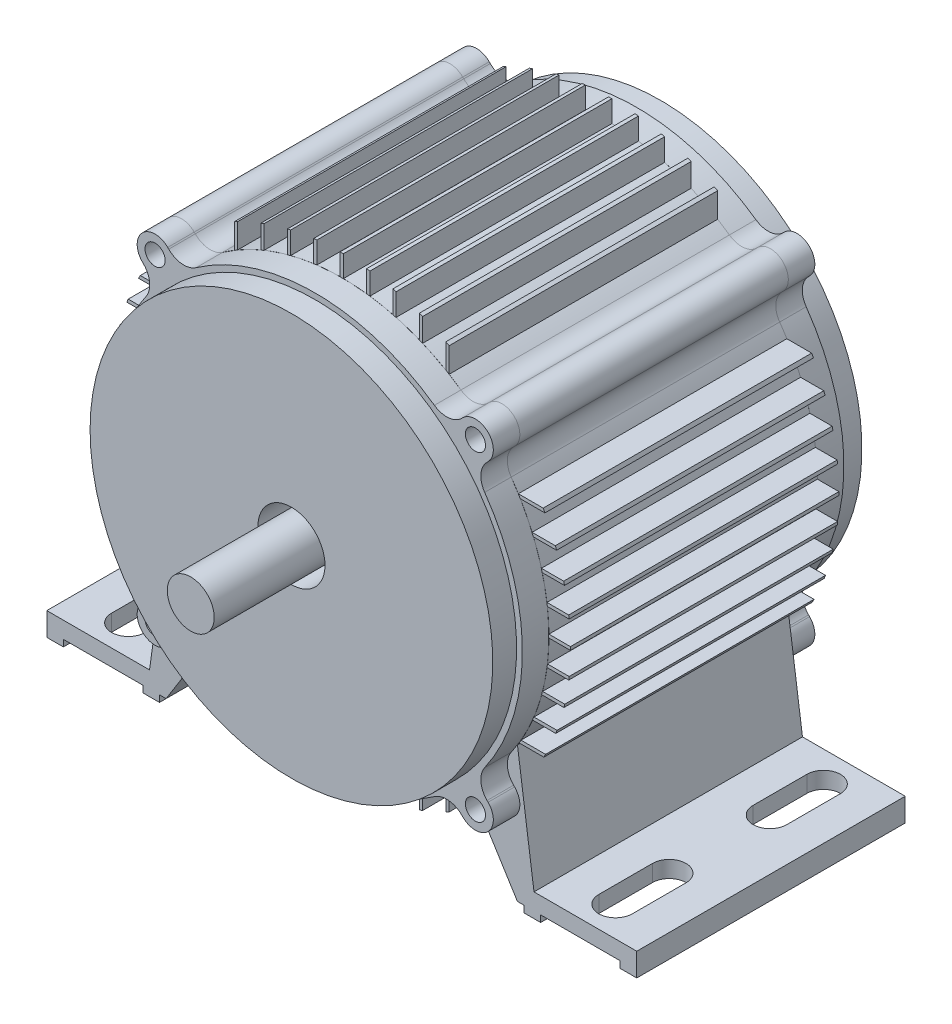
SolidWorks part; units mm, degrees
ref_plane "Front Plane" through (0, 0, 0) normal (0, 0, 1) x (1, 0, 0)
ref_plane "Top Plane" through (0, 0, 0) normal (0, 1, 0) x (1, 0, 0)
ref_plane "Right Plane" through (0, 0, 0) normal (1, 0, 0) x (0, 0, -1)
sketch "Sketch1" plane through (0, 0, 0) normal (0, 0, 1) x (1, 0, 0)
  line L0 (87.9012, -68.1481) -> (57.284, -68.1481)
  line L1 (57.284, -68.1481) -> (52.3831, -32.8719)
  line L2 (52.3831, -32.8719) -> (52.4975, -32.5422)
  line L3 (52.4975, -32.5422) -> (52.705, -32.1337)
  line L4 (52.705, -32.1337) -> (52.7419, -32.0731)
  line L5 (52.7419, -32.0731) -> (52.8389, -31.9131)
  line L6 (52.8389, -31.9131) -> (60.214, -31.9131)
  line L7 (60.214, -31.9131) -> (60.2859, -31.7771)
  line L8 (60.2859, -31.7771) -> (60.2859, -30.9254)
  line L9 (60.2859, -30.9254) -> (53.423, -30.9254)
  line L10 (53.423, -30.9254) -> (56.618, -24.5926)
  line L11 (56.618, -24.5926) -> (56.8668, -24.0119)
  line L12 (56.8668, -24.0119) -> (63.713, -24.0119)
  line L13 (63.713, -24.0119) -> (63.713, -23.0242)
  line L14 (63.713, -23.0242) -> (57.2738, -23.0242)
  line L15 (57.2738, -23.0242) -> (59.4393, -16.6541)
  line L16 (59.4393, -16.6541) -> (59.589, -16.1106)
  line L17 (59.589, -16.1106) -> (66.0327, -16.1106)
  line L18 (66.0327, -16.1106) -> (66.0327, -15.123)
  line L19 (66.0327, -15.123) -> (59.8472, -15.123)
  line L20 (59.8472, -15.123) -> (61.1535, -8.4053)
  line L21 (61.1535, -8.4053) -> (61.1669, -8.3066)
  line L22 (61.1669, -8.3066) -> (67.3482, -8.3066)
  line L23 (67.3482, -8.3066) -> (67.3482, -7.3189)
  line L24 (67.3482, -7.3189) -> (61.293, -7.3189)
  line L25 (61.293, -7.3189) -> (61.7271, -0.4053)
  line L26 (61.7271, -0.4053) -> (67.752, -0.4053)
  line L27 (67.752, -0.4053) -> (67.752, 0.5823)
  line L28 (67.752, 0.5823) -> (61.7257, 0.5823)
  line L29 (61.7257, 0.5823) -> (61.2716, 7.4959)
  line L30 (61.2716, 7.4959) -> (67.3482, 7.4959)
  line L31 (67.3482, 7.4959) -> (67.3482, 8.4836)
  line L32 (67.3482, 8.4836) -> (61.1427, 8.4836)
  line L33 (61.1427, 8.4836) -> (59.7569, 15.4762)
  line L34 (59.7569, 15.4762) -> (65.992, 15.4762)
  line L35 (65.992, 15.4762) -> (65.992, 16.4639)
  line L36 (65.992, 16.4639) -> (59.4923, 16.4639)
  line L37 (59.4923, 16.4639) -> (59.4393, 16.6541)
  line L38 (59.4393, 16.6541) -> (57.1305, 23.3775)
  line L39 (57.1305, 23.3775) -> (63.6491, 23.3775)
  line L40 (63.6491, 23.3775) -> (63.6491, 24.3509)
  line L41 (63.6491, 24.3509) -> (63.6436, 24.3651)
  line L42 (63.6436, 24.3651) -> (56.7163, 24.3651)
  line L43 (56.7163, 24.3651) -> (56.618, 24.5927)
  line L44 (56.618, 24.5927) -> (53.2169, 31.2787)
  line L45 (53.2169, 31.2787) -> (60.2458, 31.2787)
  line L46 (60.2458, 31.2787) -> (60.2459, 31.853)
  line L47 (60.2459, 31.853) -> (60.0255, 32.2664)
  line L48 (60.0255, 32.2664) -> (52.6239, 32.2664)
  line L49 (52.6239, 32.2664) -> (50.07, 36.1025)
  line L50 (50.07, 36.1025) -> (49.9817, 36.356)
  line L51 (49.9817, 36.356) -> (49.6732, 38.3039)
  line L52 (49.6732, 38.3039) -> (49.9817, 40.2519)
  line L53 (49.9817, 40.2519) -> (50.8771, 42.0093)
  line L54 (50.8771, 42.0093) -> (51.5195, 42.7614)
  line L55 (51.5195, 42.7614) -> (52.1506, 43.5004)
  line L56 (52.1506, 43.5004) -> (53.0302, 45.2268)
  line L57 (53.0302, 45.2268) -> (53.3334, 47.1404)
  line L58 (53.3334, 47.1404) -> (53.0302, 49.0541)
  line L59 (53.0302, 49.0541) -> (52.1506, 50.7805)
  line L60 (52.1506, 50.7805) -> (50.7805, 52.1506)
  line L61 (50.7805, 52.1506) -> (49.0542, 53.0302)
  line L62 (49.0542, 53.0302) -> (47.1404, 53.3334)
  line L63 (47.1404, 53.3334) -> (45.2268, 53.0303)
  line L64 (45.2268, 53.0303) -> (43.5003, 52.1506)
  line L65 (43.5003, 52.1506) -> (42.7615, 51.5195)
  line L66 (42.7615, 51.5195) -> (42.0093, 50.8771)
  line L67 (42.0093, 50.8771) -> (40.2519, 49.9816)
  line L68 (40.2519, 49.9816) -> (38.3039, 49.6731)
  line L69 (38.3039, 49.6731) -> (36.356, 49.9817)
  line L70 (36.356, 49.9817) -> (36.1025, 50.07)
  line L71 (36.1025, 50.07) -> (35.5976, 50.4303)
  line L72 (35.5976, 50.4303) -> (32.178, 52.6781)
  line L73 (32.178, 52.6781) -> (32.178, 60.0729)
  line L74 (32.178, 60.0729) -> (31.3526, 60.5077)
  line L75 (31.3526, 60.5077) -> (31.1903, 60.5916)
  line L76 (31.1903, 60.5916) -> (31.1903, 53.2688)
  line L77 (31.1903, 53.2688) -> (28.3991, 54.8077)
  line L78 (28.3991, 54.8077) -> (24.2767, 56.7542)
  line L79 (24.2767, 56.7542) -> (24.2767, 63.6774)
  line L80 (24.2767, 63.6774) -> (23.2891, 64.0452)
  line L81 (23.2891, 64.0452) -> (23.2891, 57.1665)
  line L82 (23.2891, 57.1665) -> (20.6716, 58.1642)
  line L83 (20.6716, 58.1642) -> (16.3755, 59.5167)
  line L84 (16.3755, 59.5167) -> (16.3755, 66.1514)
  line L85 (16.3755, 66.1514) -> (15.3879, 66.3882)
  line L86 (15.3879, 66.3882) -> (15.3878, 59.7796)
  line L87 (15.3878, 59.7796) -> (12.559, 60.4373)
  line L88 (12.559, 60.4373) -> (8.3951, 61.1549)
  line L89 (8.3951, 61.1549) -> (8.3951, 67.6291)
  line L90 (8.3951, 67.6291) -> (7.4074, 67.7444)
  line L91 (7.4074, 67.7444) -> (7.4074, 61.2824)
  line L92 (7.4074, 61.2824) -> (4.2125, 61.5845)
  line L93 (4.2125, 61.5845) -> (0.4938, 61.7264)
  line L94 (0.4938, 61.7264) -> (0.4938, 68.1464)
  line L95 (0.4938, 68.1464) -> (-0.4938, 68.1464)
  line L96 (-0.4938, 68.1464) -> (-0.4938, 61.7264)
  line L97 (-0.4938, 61.7264) -> (-4.2124, 61.5845)
  line L98 (-4.2124, 61.5845) -> (-7.4074, 61.2824)
  line L99 (-7.4074, 61.2824) -> (-7.4074, 67.7444)
  line L100 (-7.4074, 67.7444) -> (-8.3951, 67.6291)
  line L101 (-8.3951, 67.6291) -> (-8.3951, 61.1549)
  line L102 (-8.3951, 61.1549) -> (-12.559, 60.4373)
  line L103 (-12.559, 60.4373) -> (-15.2114, 59.8248)
  line L104 (-15.2114, 59.8248) -> (-15.2114, 66.4288)
  line L105 (-15.2114, 66.4288) -> (-16.199, 66.1949)
  line L106 (-16.199, 66.1949) -> (-16.199, 59.565)
  line L107 (-16.199, 59.565) -> (-20.6716, 58.1642)
  line L108 (-20.6716, 58.1642) -> (-23.1126, 57.2381)
  line L109 (-23.1126, 57.2381) -> (-23.1126, 64.1091)
  line L110 (-23.1126, 64.1091) -> (-24.1002, 63.7444)
  line L111 (-24.1002, 63.7444) -> (-24.1003, 56.8294)
  line L112 (-24.1003, 56.8294) -> (-28.399, 54.8078)
  line L113 (-28.399, 54.8078) -> (-31.0138, 53.3717)
  line L114 (-31.0138, 53.3717) -> (-31.0138, 60.6755)
  line L115 (-31.0138, 60.6755) -> (-31.0267, 60.6755)
  line L116 (-31.0267, 60.6755) -> (-31.3526, 60.5077)
  line L117 (-31.3526, 60.5077) -> (-32.0015, 60.167)
  line L118 (-32.0015, 60.167) -> (-32.0015, 52.7854)
  line L119 (-32.0015, 52.7854) -> (-35.5975, 50.4302)
  line L120 (-35.5975, 50.4302) -> (-36.1024, 50.0701)
  line L121 (-36.1024, 50.0701) -> (-36.3559, 49.9817)
  line L122 (-36.3559, 49.9817) -> (-38.3039, 49.6731)
  line L123 (-38.3039, 49.6731) -> (-40.2519, 49.9816)
  line L124 (-40.2519, 49.9816) -> (-42.0092, 50.877)
  line L125 (-42.0092, 50.877) -> (-42.7614, 51.5195)
  line L126 (-42.7614, 51.5195) -> (-43.5003, 52.1506)
  line L127 (-43.5003, 52.1506) -> (-45.2268, 53.0303)
  line L128 (-45.2268, 53.0303) -> (-47.1404, 53.3334)
  line L129 (-47.1404, 53.3334) -> (-49.0541, 53.0303)
  line L130 (-49.0541, 53.0303) -> (-50.7805, 52.1506)
  line L131 (-50.7805, 52.1506) -> (-52.1506, 50.7805)
  line L132 (-52.1506, 50.7805) -> (-53.0302, 49.0541)
  line L133 (-53.0302, 49.0541) -> (-53.3333, 47.1404)
  line L134 (-53.3333, 47.1404) -> (-53.0302, 45.2268)
  line L135 (-53.0302, 45.2268) -> (-52.1506, 43.5004)
  line L136 (-52.1506, 43.5004) -> (-51.5195, 42.7614)
  line L137 (-51.5195, 42.7614) -> (-50.877, 42.0093)
  line L138 (-50.877, 42.0093) -> (-49.9816, 40.2519)
  line L139 (-49.9816, 40.2519) -> (-49.6731, 38.3039)
  line L140 (-49.6731, 38.3039) -> (-49.9816, 36.3559)
  line L141 (-49.9816, 36.3559) -> (-50.07, 36.1025)
  line L142 (-50.07, 36.1025) -> (-52.6239, 32.2664)
  line L143 (-52.6239, 32.2664) -> (-60.0254, 32.2664)
  line L144 (-60.0254, 32.2664) -> (-60.5459, 31.2787)
  line L145 (-60.5459, 31.2787) -> (-53.2169, 31.2787)
  line L146 (-53.2169, 31.2787) -> (-56.6179, 24.5927)
  line L147 (-56.6179, 24.5927) -> (-56.7162, 24.3651)
  line L148 (-56.7162, 24.3651) -> (-63.6436, 24.3651)
  line L149 (-63.6436, 24.3651) -> (-64.0129, 23.3775)
  line L150 (-64.0129, 23.3775) -> (-57.1304, 23.3775)
  line L151 (-57.1304, 23.3775) -> (-59.4393, 16.6541)
  line L152 (-59.4393, 16.6541) -> (-59.4923, 16.4639)
  line L153 (-59.4923, 16.4639) -> (-66.1295, 16.4639)
  line L154 (-66.1295, 16.4639) -> (-66.3676, 15.4762)
  line L155 (-66.3676, 15.4762) -> (-59.7569, 15.4762)
  line L156 (-59.7569, 15.4762) -> (-61.1426, 8.4836)
  line L157 (-61.1426, 8.4836) -> (-67.6181, 8.4836)
  line L158 (-67.6181, 8.4836) -> (-67.7346, 7.4959)
  line L159 (-67.7346, 7.4959) -> (-61.2716, 7.4959)
  line L160 (-61.2716, 7.4959) -> (-61.7256, 0.5823)
  line L161 (-61.7256, 0.5823) -> (-68.1457, 0.5823)
  line L162 (-68.1457, 0.5823) -> (-68.1481, 0)
  line L163 (-68.1481, 0) -> (-68.147, -0.4053)
  line L164 (-68.147, -0.4053) -> (-61.727, -0.4053)
  line L165 (-61.727, -0.4053) -> (-61.293, -7.3189)
  line L166 (-61.293, -7.3189) -> (-67.754, -7.3189)
  line L167 (-67.754, -7.3189) -> (-67.64, -8.3066)
  line L168 (-67.64, -8.3066) -> (-61.1669, -8.3066)
  line L169 (-61.1669, -8.3066) -> (-61.1534, -8.4053)
  line L170 (-61.1534, -8.4053) -> (-59.8472, -15.123)
  line L171 (-59.8472, -15.123) -> (-66.449, -15.123)
  line L172 (-66.449, -15.123) -> (-66.2164, -16.1106)
  line L173 (-66.2164, -16.1106) -> (-59.5889, -16.1106)
  line L174 (-59.5889, -16.1106) -> (-59.4393, -16.6541)
  line L175 (-59.4393, -16.6541) -> (-57.2737, -23.0242)
  line L176 (-57.2737, -23.0242) -> (-64.1409, -23.0242)
  line L177 (-64.1409, -23.0242) -> (-63.7778, -24.0118)
  line L178 (-63.7778, -24.0118) -> (-56.8667, -24.0119)
  line L179 (-56.8667, -24.0119) -> (-56.618, -24.5926)
  line L180 (-56.618, -24.5926) -> (-53.4229, -30.9254)
  line L181 (-53.4229, -30.9254) -> (-60.7271, -30.9254)
  line L182 (-60.7271, -30.9254) -> (-60.2139, -31.9131)
  line L183 (-60.2139, -31.9131) -> (-52.8389, -31.9131)
  line L184 (-52.8389, -31.9131) -> (-52.7419, -32.0731)
  line L185 (-52.7419, -32.0731) -> (-52.6941, -32.1515)
  line L186 (-52.6941, -32.1515) -> (-52.486, -32.5609)
  line L187 (-52.486, -32.5609) -> (-52.3812, -32.8579)
  line L188 (-52.3812, -32.8579) -> (-57.284, -68.1481)
  line L189 (-57.284, -68.1481) -> (-87.9012, -68.1481)
  line L190 (-87.9012, -68.1481) -> (-87.9012, -75.0617)
  line L191 (-87.9012, -75.0617) -> (-82.963, -75.0617)
  line L192 (-82.963, -75.0617) -> (-82.963, -73.0864)
  line L193 (-82.963, -73.0864) -> (-59.2593, -73.0864)
  line L194 (-59.2593, -73.0864) -> (-59.2593, -75.0617)
  line L195 (-59.2593, -75.0617) -> (-54.321, -75.0617)
  line L196 (-54.321, -75.0617) -> (-54.321, -73.0864)
  line L197 (-54.321, -73.0864) -> (-52.3457, -73.0864)
  line L198 (-52.3457, -73.0864) -> (-37.7288, -49.6994)
  line L199 (-37.7288, -49.6994) -> (-36.3558, -49.9816)
  line L200 (-36.3558, -49.9816) -> (-36.1024, -50.07)
  line L201 (-36.1024, -50.07) -> (-35.5975, -50.4302)
  line L202 (-35.5975, -50.4302) -> (-32.0015, -52.7854)
  line L203 (-32.0015, -52.7854) -> (-32.0015, -60.167)
  line L204 (-32.0015, -60.167) -> (-31.3526, -60.5077)
  line L205 (-31.3526, -60.5077) -> (-31.0138, -60.682)
  line L206 (-31.0138, -60.682) -> (-31.0138, -53.3717)
  line L207 (-31.0138, -53.3717) -> (-28.399, -54.8077)
  line L208 (-28.399, -54.8077) -> (-24.1002, -56.8293)
  line L209 (-24.1002, -56.8293) -> (-24.1002, -63.7444)
  line L210 (-24.1002, -63.7444) -> (-23.1126, -64.1091)
  line L211 (-23.1126, -64.1091) -> (-23.1126, -57.2381)
  line L212 (-23.1126, -57.2381) -> (-20.6716, -58.1642)
  line L213 (-20.6716, -58.1642) -> (-16.199, -59.565)
  line L214 (-16.199, -59.565) -> (-16.199, -66.1949)
  line L215 (-16.199, -66.1949) -> (-15.2114, -66.4288)
  line L216 (-15.2114, -66.4288) -> (-15.2114, -59.8248)
  line L217 (-15.2114, -59.8248) -> (-12.559, -60.4373)
  line L218 (-12.559, -60.4373) -> (-8.3951, -61.1548)
  line L219 (-8.3951, -61.1548) -> (-8.3951, -67.6291)
  line L220 (-8.3951, -67.6291) -> (-7.4074, -67.7444)
  line L221 (-7.4074, -67.7444) -> (-7.4074, -61.2823)
  line L222 (-7.4074, -61.2823) -> (-4.2124, -61.5845)
  line L223 (-4.2124, -61.5845) -> (-0.4938, -61.7264)
  line L224 (-0.4938, -61.7264) -> (-0.4938, -68.1464)
  line L225 (-0.4938, -68.1464) -> (0.4938, -68.1464)
  line L226 (0.4938, -68.1464) -> (0.4938, -61.7264)
  line L227 (0.4938, -61.7264) -> (4.2125, -61.5845)
  line L228 (4.2125, -61.5845) -> (7.4074, -61.2823)
  line L229 (7.4074, -61.2823) -> (7.4074, -67.7444)
  line L230 (7.4074, -67.7444) -> (8.3951, -67.6291)
  line L231 (8.3951, -67.6291) -> (8.3951, -61.1548)
  line L232 (8.3951, -61.1548) -> (12.559, -60.4372)
  line L233 (12.559, -60.4372) -> (15.3879, -59.7796)
  line L234 (15.3879, -59.7796) -> (15.3879, -66.3882)
  line L235 (15.3879, -66.3882) -> (16.3755, -66.1514)
  line L236 (16.3755, -66.1514) -> (16.3755, -59.5167)
  line L237 (16.3755, -59.5167) -> (20.6716, -58.1643)
  line L238 (20.6716, -58.1643) -> (23.2891, -57.1665)
  line L239 (23.2891, -57.1665) -> (23.2891, -64.0452)
  line L240 (23.2891, -64.0452) -> (24.2767, -63.6774)
  line L241 (24.2767, -63.6774) -> (24.2767, -56.7542)
  line L242 (24.2767, -56.7542) -> (28.3991, -54.8077)
  line L243 (28.3991, -54.8077) -> (31.1903, -53.2687)
  line L244 (31.1903, -53.2687) -> (31.1903, -60.5915)
  line L245 (31.1903, -60.5915) -> (31.3526, -60.5077)
  line L246 (31.3526, -60.5077) -> (32.178, -60.0729)
  line L247 (32.178, -60.0729) -> (32.178, -52.678)
  line L248 (32.178, -52.678) -> (35.5976, -50.4303)
  line L249 (35.5976, -50.4303) -> (36.2231, -49.9828)
  line L250 (36.2231, -49.9828) -> (36.2811, -49.9636)
  line L251 (36.2811, -49.9636) -> (37.7132, -49.6743)
  line L252 (37.7132, -49.6743) -> (52.3457, -73.0864)
  line L253 (52.3457, -73.0864) -> (54.321, -73.0864)
  line L254 (54.321, -73.0864) -> (54.321, -75.0617)
  line L255 (54.321, -75.0617) -> (59.2593, -75.0617)
  line L256 (59.2593, -75.0617) -> (59.2593, -73.0864)
  line L257 (59.2593, -73.0864) -> (82.963, -73.0864)
  line L258 (82.963, -73.0864) -> (82.963, -75.0617)
  line L259 (82.963, -75.0617) -> (87.9012, -75.0617)
  line L260 (87.9012, -75.0617) -> (87.9012, -68.1481)
  line L261 (0, -68.1464) -> (0, 68.1464) construction
sketch "Sketch2" plane through (0, 0, 0) normal (0, 0, 1) x (1, 0, 0)
  line L0 (0, 0) -> (0, 81.9085) construction
  line L1 (-45.607, 45.607) -> (-81.6783, 81.6783) construction
  line L2 (0, 0) -> (-32.0015, 32.0015) construction
  line L3 (0, 0) -> (-81.6783, 81.6783) construction
  line L4 (-32.0015, 60.167) -> (-32.0015, 52.7854) construction
  line L5 (-51.1961, 43.6527) -> (-51.5014, 43.958)
  line L6 (-43.6527, 51.1961) -> (-43.958, 51.5014)
  line L7 (-31.0138, 53.3717) -> (-31.0138, 60.6755) construction
  line L8 (-3.7717, -3.7717) -> (-85.45, 77.9066) construction
  line L9 (0, 0) -> (0, -101.5619) construction
  line L10 (-24.1002, 63.7444) -> (-24.1003, 56.8294) construction
  line L11 (-23.1126, 57.2381) -> (-23.1126, 64.1091) construction
  line L12 (-16.199, 66.1949) -> (-16.199, 59.565) construction
  line L13 (-15.2114, 59.8248) -> (-15.2114, 66.4288) construction
  line L14 (-8.3951, 67.6291) -> (-8.3951, 61.1549) construction
  line L15 (-7.4074, 61.2824) -> (-7.4074, 67.7444) construction
  line L16 (-0.4938, 68.1464) -> (-0.4938, 61.7264) construction
  line L17 (-52.6239, 32.2664) -> (-60.0254, 32.2664) construction
  line L18 (-60.5459, 31.2787) -> (-53.2169, 31.2787) construction
  line L19 (-56.7162, 24.3651) -> (-63.6436, 24.3651) construction
  line L20 (-64.0129, 23.3775) -> (-57.1304, 23.3775) construction
  line L21 (-59.4923, 16.4639) -> (-66.1295, 16.4639) construction
  line L22 (-66.3676, 15.4762) -> (-59.7569, 15.4762) construction
  line L23 (-61.1426, 8.4836) -> (-67.6181, 8.4836) construction
  line L24 (-67.7346, 7.4959) -> (-61.2716, 7.4959) construction
  line L25 (-61.7256, 0.5823) -> (-68.1457, 0.5823) construction
  line L26 (-68.147, -0.4053) -> (-61.727, -0.4053) construction
  line L27 (-61.293, -7.3189) -> (-67.754, -7.3189) construction
  line L28 (-67.64, -8.3066) -> (-61.1669, -8.3066) construction
  line L29 (-59.8472, -15.123) -> (-66.449, -15.123) construction
  line L30 (-66.2164, -16.1106) -> (-59.5889, -16.1106) construction
  line L31 (-57.2737, -23.0242) -> (-64.1409, -23.0242) construction
  line L32 (-63.7778, -24.0118) -> (-56.8667, -24.0119) construction
  line L33 (-53.4229, -30.9254) -> (-60.7271, -30.9254) construction
  line L34 (-60.2139, -31.9131) -> (-52.8389, -31.9131) construction
  line L35 (-52.3812, -32.8579) -> (-57.284, -68.1481) construction
  line L36 (-52.3457, -73.0864) -> (-37.7288, -49.6994) construction
  line L37 (-54.321, -73.0864) -> (-52.3457, -73.0864) construction
  line L38 (-54.321, -75.0617) -> (-54.321, -73.0864) construction
  line L39 (-59.2593, -75.0617) -> (-54.321, -75.0617) construction
  line L40 (-59.2593, -73.0864) -> (-59.2593, -75.0617) construction
  line L41 (-82.963, -73.0864) -> (-59.2593, -73.0864) construction
  line L42 (-57.284, -68.1481) -> (-87.9012, -68.1481) construction
  line L43 (-87.9012, -68.1481) -> (-87.9012, -75.0617) construction
  line L44 (-87.9012, -75.0617) -> (-82.963, -75.0617) construction
  line L45 (-82.963, -75.0617) -> (-82.963, -73.0864) construction
  line L46 (-32.0015, -52.7854) -> (-32.0015, -60.167) construction
  line L47 (-31.0138, -60.682) -> (-31.0138, -53.3717) construction
  line L48 (-24.1002, -56.8293) -> (-24.1002, -63.7444) construction
  line L49 (-23.1126, -64.1091) -> (-23.1126, -57.2381) construction
  line L50 (-16.199, -59.565) -> (-16.199, -66.1949) construction
  line L51 (-15.2114, -66.4288) -> (-15.2114, -59.8248) construction
  line L52 (-8.3951, -61.1548) -> (-8.3951, -67.6291) construction
  line L53 (-7.4074, -67.7444) -> (-7.4074, -61.2823) construction
  line L54 (-0.4938, -61.7264) -> (-0.4938, -68.1464) construction
  line L55 (-32.0015, 60.167) -> (-32.0015, 52.7854)
  line L56 (-31.0138, 53.3717) -> (-31.0138, 60.6801)
  line L57 (-24.1002, 63.7444) -> (-24.1003, 56.8293)
  line L58 (-23.1126, 57.2381) -> (-23.1126, 64.1091)
  line L59 (-16.199, 66.1949) -> (-16.199, 59.565)
  line L60 (-15.2114, 59.8248) -> (-15.2114, 66.4288)
  line L61 (-8.3951, 67.6291) -> (-8.3951, 61.1549)
  line L62 (-7.4074, 61.2823) -> (-7.4074, 67.7444)
  line L63 (-0.4938, 68.1464) -> (-0.4938, 61.7264)
  line L64 (-52.6239, 32.2664) -> (-60.0254, 32.2664)
  line L65 (-60.5459, 31.2787) -> (-53.2169, 31.2787)
  line L66 (-56.7163, 24.3651) -> (-63.6436, 24.3651)
  line L67 (-64.0129, 23.3775) -> (-57.1305, 23.3775)
  line L68 (-59.4923, 16.4639) -> (-66.1295, 16.4639)
  line L69 (-66.3676, 15.4762) -> (-59.7569, 15.4762)
  line L70 (-61.1427, 8.4836) -> (-67.6181, 8.4836)
  line L71 (-67.7346, 7.4959) -> (-61.2716, 7.4959)
  line L72 (-61.7256, 0.5823) -> (-68.1457, 0.5823)
  line L73 (-68.147, -0.4053) -> (-61.7271, -0.4053)
  line L74 (-61.293, -7.3189) -> (-67.754, -7.3189)
  line L75 (-67.64, -8.3066) -> (-61.167, -8.3066)
  line L76 (-59.8472, -15.123) -> (-66.449, -15.123)
  line L77 (-66.2164, -16.1106) -> (-59.5889, -16.1106)
  line L78 (-57.2737, -23.0242) -> (-64.1409, -23.0242)
  line L79 (-63.7778, -24.0118) -> (-56.8667, -24.0119)
  line L80 (-53.423, -30.9254) -> (-60.7271, -30.9254)
  line L81 (-60.2139, -31.9131) -> (-52.8389, -31.9131)
  line L82 (-52.3586, -32.6952) -> (-57.284, -68.1481)
  line L83 (-52.3457, -73.0864) -> (-37.3725, -49.1293)
  line L84 (-54.321, -73.0864) -> (-52.3457, -73.0864)
  line L85 (-54.321, -75.0617) -> (-54.321, -73.0864)
  line L86 (-59.2593, -75.0617) -> (-54.321, -75.0617)
  line L87 (-59.2593, -73.0864) -> (-59.2593, -75.0617)
  line L88 (-82.963, -73.0864) -> (-59.2593, -73.0864)
  line L89 (-57.284, -68.1481) -> (-87.9012, -68.1481)
  line L90 (-87.9012, -68.1481) -> (-87.9012, -75.0617)
  line L91 (-87.9012, -75.0617) -> (-82.963, -75.0617)
  line L92 (-82.963, -75.0617) -> (-82.963, -73.0864)
  line L93 (-32.0015, -52.7854) -> (-32.0015, -60.167)
  line L94 (-31.0138, -60.682) -> (-31.0138, -53.3717)
  line L95 (-24.1002, -56.8293) -> (-24.1002, -63.7444)
  line L96 (-23.1126, -64.1091) -> (-23.1126, -57.2381)
  line L97 (-16.199, -59.565) -> (-16.199, -66.1949)
  line L98 (-15.2114, -66.4288) -> (-15.2114, -59.8248)
  line L99 (-8.3951, -61.1549) -> (-8.3951, -67.6291)
  line L100 (-7.4074, -67.7444) -> (-7.4074, -61.2823)
  line L101 (-0.4938, -61.7264) -> (-0.4938, -68.1464)
  line L102 (0, 0) -> (32.0015, 32.0015) construction
  line L103 (45.607, 45.607) -> (81.6783, 81.6783) construction
  line L104 (0.4938, -61.7264) -> (0.4938, -68.1464)
  line L105 (7.4074, -67.7444) -> (7.4074, -61.2823)
  line L106 (8.3951, -61.1549) -> (8.3951, -67.6291)
  line L107 (15.2114, -66.4288) -> (15.2114, -59.8248)
  line L108 (16.199, -59.565) -> (16.199, -66.1949)
  line L109 (23.1126, -64.1091) -> (23.1126, -57.2381)
  line L110 (24.1002, -56.8293) -> (24.1002, -63.7444)
  line L111 (31.0138, -60.682) -> (31.0138, -53.3717)
  line L112 (32.0015, -52.7854) -> (32.0015, -60.167)
  line L113 (82.963, -75.0617) -> (82.963, -73.0864)
  line L114 (87.9012, -75.0617) -> (82.963, -75.0617)
  line L115 (87.9012, -68.1481) -> (87.9012, -75.0617)
  line L116 (57.284, -68.1481) -> (87.9012, -68.1481)
  line L117 (82.963, -73.0864) -> (59.2593, -73.0864)
  line L118 (59.2593, -73.0864) -> (59.2593, -75.0617)
  line L119 (59.2593, -75.0617) -> (54.321, -75.0617)
  line L120 (54.321, -75.0617) -> (54.321, -73.0864)
  line L121 (54.321, -73.0864) -> (52.3457, -73.0864)
  line L122 (52.3457, -73.0864) -> (37.3725, -49.1293)
  line L123 (52.3586, -32.6952) -> (57.284, -68.1481)
  line L124 (60.2139, -31.9131) -> (52.8389, -31.9131)
  line L125 (53.423, -30.9254) -> (60.7271, -30.9254)
  line L126 (63.7778, -24.0118) -> (56.8667, -24.0119)
  line L127 (57.2737, -23.0242) -> (64.1409, -23.0242)
  line L128 (66.2164, -16.1106) -> (59.5889, -16.1106)
  line L129 (59.8472, -15.123) -> (66.449, -15.123)
  line L130 (67.64, -8.3066) -> (61.167, -8.3066)
  line L131 (61.293, -7.3189) -> (67.754, -7.3189)
  line L132 (68.147, -0.4053) -> (61.7271, -0.4053)
  line L133 (61.7256, 0.5823) -> (68.1457, 0.5823)
  line L134 (67.7346, 7.4959) -> (61.2716, 7.4959)
  line L135 (61.1427, 8.4836) -> (67.6181, 8.4836)
  line L136 (66.3676, 15.4762) -> (59.7569, 15.4762)
  line L137 (59.4923, 16.4639) -> (66.1295, 16.4639)
  line L138 (64.0129, 23.3775) -> (57.1305, 23.3775)
  line L139 (56.7163, 24.3651) -> (63.6436, 24.3651)
  line L140 (60.5459, 31.2787) -> (53.2169, 31.2787)
  line L141 (52.6239, 32.2664) -> (60.0254, 32.2664)
  line L142 (0.4938, 68.1464) -> (0.4938, 61.7264)
  line L143 (7.4074, 61.2823) -> (7.4074, 67.7444)
  line L144 (8.3951, 67.6291) -> (8.3951, 61.1549)
  line L145 (15.2114, 59.8248) -> (15.2114, 66.4288)
  line L146 (16.199, 66.1949) -> (16.199, 59.565)
  line L147 (23.1126, 57.2381) -> (23.1126, 64.1091)
  line L148 (24.1002, 63.7444) -> (24.1003, 56.8293)
  line L149 (31.0138, 53.3717) -> (31.0138, 60.6801)
  line L150 (32.0015, 60.167) -> (32.0015, 52.7854)
  line L151 (43.6527, 51.1961) -> (43.958, 51.5014)
  line L152 (51.1961, 43.6527) -> (51.5014, 43.958)
  arc A0 (-50.4921, 35.5097) -> (-52.6239, 32.2664) centre (0, 0) ccw
  circle A1 centre (-47.7297, 47.7297) radius 3.0019
  arc A2 (-43.958, 51.5014) -> (-51.5014, 43.958) centre (-47.7297, 47.7297) ccw
  arc A3 (-0.4938, 61.7264) -> (-7.4074, 61.2823) centre (0, 0) ccw
  arc A4 (-43.6527, 51.1961) -> (-35.5097, 50.4921) centre (-39.1626, 55.6863) ccw
  arc A5 (-51.1961, 43.6527) -> (-50.4921, 35.5097) centre (-55.6863, 39.1626) cw
  arc A6 (0.4938, 68.1446) -> (-0.4938, 68.1446) centre (0, 0) ccw
  arc A7 (-32.0015, -60.165) -> (-31.0138, -60.6801) centre (0, 0) ccw
  arc A8 (-24.1002, -63.7425) -> (-23.1126, -64.1072) centre (0, 0) ccw
  arc A9 (-16.199, -66.193) -> (-15.2114, -66.427) centre (0, 0) ccw
  arc A10 (-8.3951, -67.6273) -> (-7.4074, -67.7426) centre (0, 0) ccw
  arc A11 (-60.7252, -30.9254) -> (-60.212, -31.9131) centre (0, 0) ccw
  arc A12 (-64.139, -23.0242) -> (-63.7759, -24.0118) centre (0, 0) ccw
  arc A13 (-66.4471, -15.123) -> (-66.2146, -16.1106) centre (0, 0) ccw
  arc A14 (-67.7522, -7.3189) -> (-67.6382, -8.3066) centre (0, 0) ccw
  arc A15 (-68.1439, 0.5823) -> (-68.1452, -0.4053) centre (0, 0) ccw
  arc A16 (-66.1277, 16.4639) -> (-66.3658, 15.4762) centre (0, 0) ccw
  arc A17 (-63.6417, 24.3651) -> (-64.0111, 23.3775) centre (0, 0) ccw
  arc A18 (-60.0234, 32.2664) -> (-60.544, 31.2787) centre (0, 0) ccw
  arc A19 (-23.1126, 64.1072) -> (-24.1002, 63.7425) centre (0, 0) ccw
  arc A20 (-15.2114, 66.427) -> (-16.199, 66.193) centre (0, 0) ccw
  arc A21 (-7.4074, 67.7426) -> (-8.3951, 67.6273) centre (0, 0) ccw
  arc A22 (-0.4938, -68.1446) -> (0.4938, -68.1446) centre (0, 0) ccw
  arc A23 (-31.0138, 60.6801) -> (-32.0015, 60.165) centre (0, 0) ccw
  arc A24 (-67.6162, 8.4836) -> (-67.7329, 7.4959) centre (0, 0) ccw
  arc A25 (-7.4074, -61.2823) -> (-0.4938, -61.7264) centre (0, 0) ccw
  arc A26 (-15.2114, -59.8248) -> (-8.3951, -61.1549) centre (0, 0) ccw
  arc A27 (-23.1126, -57.2381) -> (-16.199, -59.565) centre (0, 0) ccw
  arc A28 (-31.0138, -53.3717) -> (-24.1002, -56.8293) centre (0, 0) ccw
  arc A29 (-37.3725, -49.1293) -> (-32.0015, -52.7854) centre (0, 0) ccw
  arc A30 (-52.8389, -31.9131) -> (-52.3586, -32.6952) centre (0, 0) ccw
  arc A31 (-56.8667, -24.0119) -> (-53.423, -30.9254) centre (0, 0) ccw
  arc A32 (-59.5889, -16.1106) -> (-57.2737, -23.0242) centre (0, 0) ccw
  arc A33 (-61.167, -8.3066) -> (-59.8472, -15.123) centre (0, 0) ccw
  arc A34 (-61.7271, -0.4053) -> (-61.293, -7.3189) centre (0, 0) ccw
  arc A35 (-61.2716, 7.4959) -> (-61.7256, 0.5823) centre (0, 0) ccw
  arc A36 (-59.7569, 15.4762) -> (-61.1427, 8.4836) centre (0, 0) ccw
  arc A37 (-57.1305, 23.3775) -> (-59.4923, 16.4639) centre (0, 0) ccw
  arc A38 (-53.2169, 31.2787) -> (-56.7163, 24.3651) centre (0, 0) ccw
  arc A39 (-32.0015, 52.7854) -> (-35.5097, 50.4921) centre (0, 0) ccw
  arc A40 (-24.1003, 56.8293) -> (-31.0138, 53.3717) centre (0, 0) ccw
  arc A41 (-16.199, 59.565) -> (-23.1126, 57.2381) centre (0, 0) ccw
  arc A42 (-8.3951, 61.1549) -> (-15.2114, 59.8248) centre (0, 0) ccw
  arc A43 (8.3951, 61.1549) -> (15.2114, 59.8248) centre (0, 0) cw
  arc A44 (16.199, 59.565) -> (23.1126, 57.2381) centre (0, 0) cw
  arc A45 (24.1003, 56.8293) -> (31.0138, 53.3717) centre (0, 0) cw
  arc A46 (32.0015, 52.7854) -> (35.5097, 50.4921) centre (0, 0) cw
  arc A47 (53.2169, 31.2787) -> (56.7163, 24.3651) centre (0, 0) cw
  arc A48 (57.1305, 23.3775) -> (59.4923, 16.4639) centre (0, 0) cw
  arc A49 (59.7569, 15.4762) -> (61.1427, 8.4836) centre (0, 0) cw
  arc A50 (61.2716, 7.4959) -> (61.7256, 0.5823) centre (0, 0) cw
  arc A51 (61.7271, -0.4053) -> (61.293, -7.3189) centre (0, 0) cw
  arc A52 (61.167, -8.3066) -> (59.8472, -15.123) centre (0, 0) cw
  arc A53 (59.5889, -16.1106) -> (57.2737, -23.0242) centre (0, 0) cw
  arc A54 (56.8667, -24.0119) -> (53.423, -30.9254) centre (0, 0) cw
  arc A55 (52.8389, -31.9131) -> (52.3586, -32.6952) centre (0, 0) cw
  arc A56 (37.3725, -49.1293) -> (32.0015, -52.7854) centre (0, 0) cw
  arc A57 (31.0138, -53.3717) -> (24.1002, -56.8293) centre (0, 0) cw
  arc A58 (23.1126, -57.2381) -> (16.199, -59.565) centre (0, 0) cw
  arc A59 (15.2114, -59.8248) -> (8.3951, -61.1549) centre (0, 0) cw
  arc A60 (7.4074, -61.2823) -> (0.4938, -61.7264) centre (0, 0) cw
  arc A61 (67.6162, 8.4836) -> (67.7329, 7.4959) centre (0, 0) cw
  arc A62 (31.0138, 60.6801) -> (32.0015, 60.165) centre (0, 0) cw
  arc A63 (7.4074, 67.7426) -> (8.3951, 67.6273) centre (0, 0) cw
  arc A64 (15.2114, 66.427) -> (16.199, 66.193) centre (0, 0) cw
  arc A65 (23.1126, 64.1072) -> (24.1002, 63.7425) centre (0, 0) cw
  arc A66 (60.0234, 32.2664) -> (60.544, 31.2787) centre (0, 0) cw
  arc A67 (63.6417, 24.3651) -> (64.0111, 23.3775) centre (0, 0) cw
  arc A68 (66.1277, 16.4639) -> (66.3658, 15.4762) centre (0, 0) cw
  arc A69 (68.1439, 0.5823) -> (68.1452, -0.4053) centre (0, 0) cw
  arc A70 (67.7522, -7.3189) -> (67.6382, -8.3066) centre (0, 0) cw
  arc A71 (66.4471, -15.123) -> (66.2146, -16.1106) centre (0, 0) cw
  arc A72 (64.139, -23.0242) -> (63.7759, -24.0118) centre (0, 0) cw
  arc A73 (60.7252, -30.9254) -> (60.212, -31.9131) centre (0, 0) cw
  arc A74 (8.3951, -67.6273) -> (7.4074, -67.7426) centre (0, 0) cw
  arc A75 (16.199, -66.193) -> (15.2114, -66.427) centre (0, 0) cw
  arc A76 (24.1002, -63.7425) -> (23.1126, -64.1072) centre (0, 0) cw
  arc A77 (32.0015, -60.165) -> (31.0138, -60.6801) centre (0, 0) cw
  arc A78 (51.1961, 43.6527) -> (50.4921, 35.5097) centre (55.6863, 39.1626) ccw
  arc A79 (43.6527, 51.1961) -> (35.5097, 50.4921) centre (39.1626, 55.6863) cw
  arc A80 (0.4938, 61.7264) -> (7.4074, 61.2823) centre (0, 0) cw
  arc A81 (43.958, 51.5014) -> (51.5014, 43.958) centre (47.7297, 47.7297) cw
  circle A82 centre (47.7297, 47.7297) radius 3.0019
  arc A83 (50.4921, 35.5097) -> (52.6239, 32.2664) centre (0, 0) cw
  dimension "D3" = 10.668
  dimension "D4" = 6.35
  dimension "D1" = 45
  dimension "D2" = 67.5
  dimension "D5" = 5.334
extrude "Boss-Extrude1" add sketch "Sketch2" along normal mid plane 80 contours A83 A78 L152 A81 L151 A79 A46 L150 A62 L149 A45 L148 A65 L147 A44 L146 A64 L145 A43 L144 A63 L143 A80 L142 A6 L63 A3 L62 A21 L61 A42 L60 A20 L59 A41 L58 A19 L57 A40 L56 A23 L55 A39 A4 L6 A2 L5 A5 A0 L64 A18
sketch "Sketch3" plane through (0, 0, -40) normal (0, 0, -1) x (-1, 0, 0)
  line L0 (-51.1961, 43.6527) -> (-51.5014, 43.958) construction
  line L1 (-43.6527, 51.1961) -> (-43.958, 51.5014) construction
  line L2 (-51.1961, 43.6527) -> (-51.5014, 43.958)
  line L3 (-43.6527, 51.1961) -> (-43.958, 51.5014)
  line L4 (43.6527, 51.1961) -> (43.958, 51.5014)
  line L5 (51.1961, 43.6527) -> (51.5014, 43.958)
  line L6 (51.1961, -43.6527) -> (51.5014, -43.958)
  line L7 (43.6527, -51.1961) -> (43.958, -51.5014)
  line L8 (-43.6527, -51.1961) -> (-43.958, -51.5014)
  line L9 (-51.1961, -43.6527) -> (-51.5014, -43.958)
  arc A0 (-50.4921, 35.5097) -> (-50.4921, -35.5097) centre (0, 0) ccw
  arc A1 (-50.4921, 35.5097) -> (-51.1961, 43.6527) centre (-55.6863, 39.1626) ccw construction
  arc A2 (-43.958, 51.5014) -> (-51.5014, 43.958) centre (-47.7297, 47.7297) ccw construction
  arc A3 (-43.6527, 51.1961) -> (-35.5097, 50.4921) centre (-39.1626, 55.6863) ccw construction
  circle A4 centre (-47.7297, 47.7297) radius 3.0019 construction
  arc A5 (-50.4921, 35.5097) -> (-51.1961, 43.6527) centre (-55.6863, 39.1626) ccw
  arc A6 (-43.958, 51.5014) -> (-51.5014, 43.958) centre (-47.7297, 47.7297) ccw
  arc A7 (-43.6527, 51.1961) -> (-35.5097, 50.4921) centre (-39.1626, 55.6863) ccw
  circle A8 centre (-47.7297, 47.7297) radius 3.0019
  arc A9 (35.5097, 50.4921) -> (43.6527, 51.1961) centre (39.1626, 55.6863) ccw
  arc A10 (51.5014, 43.958) -> (43.958, 51.5014) centre (47.7297, 47.7297) ccw
  circle A11 centre (47.7297, 47.7297) radius 3.0019
  arc A12 (51.1961, 43.6527) -> (50.4921, 35.5097) centre (55.6863, 39.1626) ccw
  arc A13 (50.4921, -35.5097) -> (51.1961, -43.6527) centre (55.6863, -39.1626) ccw
  arc A14 (43.958, -51.5014) -> (51.5014, -43.958) centre (47.7297, -47.7297) ccw
  circle A15 centre (47.7297, -47.7297) radius 3.0019
  arc A16 (43.6527, -51.1961) -> (35.5097, -50.4921) centre (39.1626, -55.6863) ccw
  arc A17 (-35.5097, -50.4921) -> (-43.6527, -51.1961) centre (-39.1626, -55.6863) ccw
  arc A18 (-51.5014, -43.958) -> (-43.958, -51.5014) centre (-47.7297, -47.7297) ccw
  circle A19 centre (-47.7297, -47.7297) radius 3.0019
  arc A20 (-51.1961, -43.6527) -> (-50.4921, -35.5097) centre (-55.6863, -39.1626) ccw
  arc A21 (35.5097, 50.4921) -> (-35.5097, 50.4921) centre (0, 0) ccw
  arc A22 (50.4921, -35.5097) -> (50.4921, 35.5097) centre (0, 0) ccw
  arc A23 (-35.5097, -50.4921) -> (35.5097, -50.4921) centre (0, 0) ccw
  point P46 (0, 0)
  dimension "D1" = 4
extrude "Boss-Extrude2" add sketch "Sketch3" along normal blind 7.9012 separate body
sketch "Sketch4" plane through (0, 0, -47.9012) normal (0, 0, -1) x (-1, 0, 0)
  circle A0 centre (0, 0) radius 60
  dimension "D1" = 120
extrude "Boss-Extrude3" add sketch "Sketch4" along normal blind 7.0988
mirror "Mirror2" about plane through (0, 0, 0) normal (0, 0, 1) of bodies 103
sketch "Sketch5" plane through (0, 0, 55) normal (0, 0, 1) x (1, 0, 0)
  circle A0 centre (0, 0) radius 10
  dimension "D1" = 20
extrude "Cut-Extrude1" cut sketch "Sketch5" against normal blind 10
sketch "Sketch6" plane through (0, 0, 45) normal (0, 0, 1) x (1, 0, 0)
  circle A0 centre (0, 0) radius 7
  dimension "D1" = 14
extrude "Boss-Extrude4" add sketch "Sketch6" along normal blind 40
sketch "Sketch7" plane through (0, -68.1481, 0) normal (0, 1, 0) x (1, 0, 0)
  line L0 (-72.5926, 31) -> (-72.5926, 15) construction
  line L1 (-67.5926, 31) -> (-67.5926, 15)
  line L2 (-77.5926, 31) -> (-77.5926, 15)
  line L3 (-57.284, 40) -> (-87.9012, 40) construction
  line L4 (-87.9012, 0) -> (87.9012, 0) construction
  line L5 (-87.9012, -40) -> (-87.9012, 40) construction
  line L6 (87.9012, -40) -> (87.9012, 40) construction
  line L7 (0, 0) -> (0, -59.9105) construction
  line L8 (-72.5926, -31) -> (-72.5926, -15) construction
  line L9 (-67.5926, -31) -> (-67.5926, -15)
  line L10 (-77.5926, -31) -> (-77.5926, -15)
  line L11 (72.5926, 31) -> (72.5926, 15) construction
  line L12 (67.5926, 31) -> (67.5926, 15)
  line L13 (77.5926, 31) -> (77.5926, 15)
  line L14 (72.5926, -31) -> (72.5926, -15) construction
  line L15 (67.5926, -31) -> (67.5926, -15)
  line L16 (77.5926, -31) -> (77.5926, -15)
  arc A0 (-67.5926, 31) -> (-77.5926, 31) centre (-72.5926, 31) ccw
  arc A1 (-77.5926, 15) -> (-67.5926, 15) centre (-72.5926, 15) ccw
  arc A2 (-67.5926, -31) -> (-77.5926, -31) centre (-72.5926, -31) cw
  arc A3 (-77.5926, -15) -> (-67.5926, -15) centre (-72.5926, -15) cw
  arc A4 (67.5926, 31) -> (77.5926, 31) centre (72.5926, 31) cw
  arc A5 (77.5926, 15) -> (67.5926, 15) centre (72.5926, 15) cw
  arc A6 (67.5926, -31) -> (77.5926, -31) centre (72.5926, -31) ccw
  arc A7 (77.5926, -15) -> (67.5926, -15) centre (72.5926, -15) ccw
  point P2 (-72.5926, 23)
  point P9 (0, 2.4585)
  point P20 (-72.5926, -23)
  point P27 (72.5926, 23)
  point P34 (72.5926, -23)
  dimension "D1" = 10
  dimension "D2" = 16
  dimension "D3" = 4
extrude "Cut-Extrude2" cut sketch "Sketch7" against normal through all
